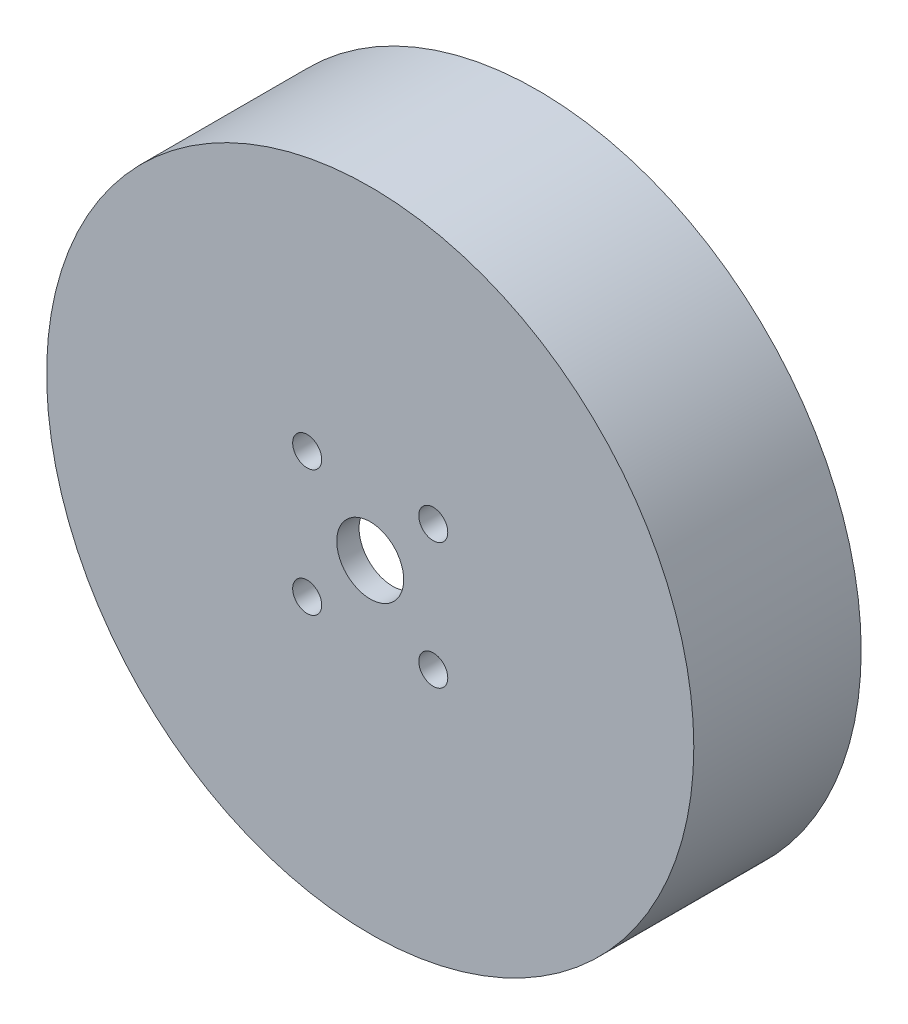
SolidWorks part; units mm, degrees
ref_plane "前视基准面" through (0, 0, 0) normal (0, 0, 1) x (1, 0, 0)
ref_plane "上视基准面" through (0, 0, 0) normal (0, 1, 0) x (1, 0, 0)
ref_plane "右视基准面" through (0, 0, 0) normal (1, 0, 0) x (0, 0, -1)
sketch "草图1" plane through (0, 0, 0) normal (0, 0, 1) x (1, 0, 0)
  circle A0 centre (0, 0) radius 29
  dimension "D1" = 58
extrude "凸台-拉伸1" add sketch "草图1" along normal blind 15
sketch "草图2" plane through (0, 0, 0) normal (0, 0, -1) x (-1, 0, 0)
  circle A0 centre (0, 0) radius 25
  dimension "D1" = 50
extrude "切除-拉伸1" cut sketch "草图2" against normal blind 13
sketch "草图3" plane through (0, 0, 15) normal (0, 0, 1) x (1, 0, 0)
  line L5 (-5.65, -5.65) -> (5.65, 5.65) construction
  line L6 (-5.65, 5.65) -> (5.65, -5.65) construction
  circle A0 centre (5.65, 5.65) radius 1.3
  circle A1 centre (5.65, -5.65) radius 1.3
  circle A2 centre (-5.65, -5.65) radius 1.3
  circle A3 centre (-5.65, 5.65) radius 1.3
  circle A4 centre (0, 0) radius 3
  point P0 (0, 0)
  dimension "D2" = 2.6
  dimension "D3" = 2.6
  dimension "D4" = 2.6
  dimension "D5" = 2.6
  dimension "D6" = 6
  dimension "D1" = 11.3
extrude "切除-拉伸2" cut sketch "草图3" against normal up to next
sketch "草图4" plane through (0, 0, 13) normal (0, 0, -1) x (-1, 0, 0)
  line L0 (0, 0) -> (55.1131, 0.8438) construction
  line L1 (-0.2641, 17.248) -> (-0.3827, 24.9971) construction
  line L5 (3.4753, 16.8963) -> (5.0367, 24.4874)
  line L6 (-3.991, 16.782) -> (-5.784, 24.3217)
  line L7 (16.3703, 5.4384) -> (23.725, 7.8818)
  line L8 (12.5381, 11.8473) -> (18.1712, 17.17)
  line L9 (12.895, -11.4579) -> (18.6883, -16.6056)
  line L10 (16.5291, -4.9347) -> (23.9552, -7.1517)
  line L11 (-3.4753, -16.8963) -> (-5.0367, -24.4874)
  line L12 (3.991, -16.782) -> (5.784, -24.3217)
  line L13 (-16.3703, -5.4384) -> (-23.725, -7.8818)
  line L14 (-12.5381, -11.8473) -> (-18.1712, -17.17)
  line L15 (-12.895, 11.4579) -> (-18.6883, 16.6056)
  line L16 (-16.5291, 4.9347) -> (-23.9552, 7.1517)
  arc A7 (5.0367, 24.4874) -> (-5.784, 24.3217) centre (0, 0) ccw
  arc A10 (3.4753, 16.8963) -> (-3.991, 16.782) centre (0, 0) ccw
  arc A11 (23.725, 7.8818) -> (18.1712, 17.17) centre (0, 0) ccw
  arc A12 (16.3703, 5.4384) -> (12.5381, 11.8473) centre (0, 0) ccw
  arc A13 (18.6883, -16.6056) -> (23.9552, -7.1517) centre (0, 0) ccw
  arc A14 (12.895, -11.4579) -> (16.5291, -4.9347) centre (0, 0) ccw
  arc A15 (-5.0367, -24.4874) -> (5.784, -24.3217) centre (0, 0) ccw
  arc A16 (-3.4753, -16.8963) -> (3.991, -16.782) centre (0, 0) ccw
  arc A17 (-23.725, -7.8818) -> (-18.1712, -17.17) centre (0, 0) ccw
  arc A18 (-16.3703, -5.4384) -> (-12.5381, -11.8473) centre (0, 0) ccw
  arc A19 (-18.6883, 16.6056) -> (-23.9552, 7.1517) centre (0, 0) ccw
  arc A20 (-12.895, 11.4579) -> (-16.5291, 4.9347) centre (0, 0) ccw
  point P31 (0, 0)
  dimension "D1" = 50
  dimension "D2" = 34.5
  dimension "D3" = 12.5
  dimension "D4" = 6
extrude "凸台-拉伸3" add sketch "草图4" along normal blind 10
